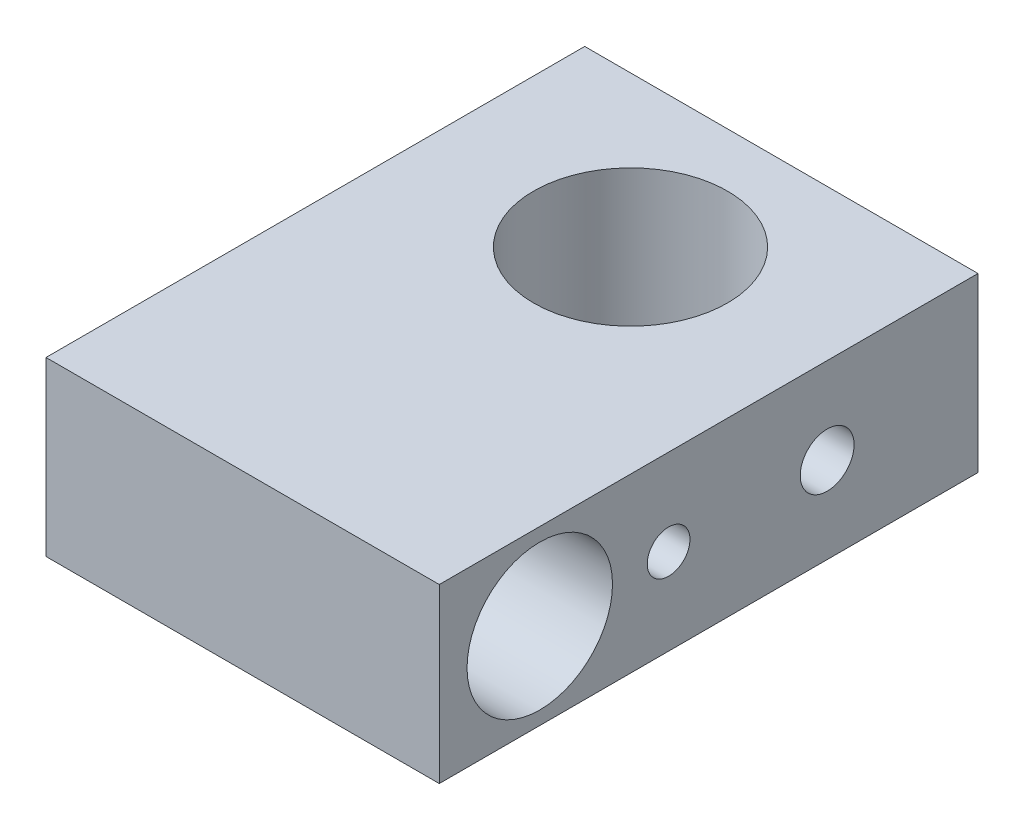
SolidWorks part; units mm, degrees
material "6061-T6 (SS)"
ref_plane "Front Plane" through (0, 0, 0) normal (0, 0, 1) x (1, 0, 0)
ref_plane "Top Plane" through (0, 0, 0) normal (0, 1, 0) x (1, 0, 0)
ref_plane "Right Plane" through (0, 0, 0) normal (1, 0, 0) x (0, 0, -1)
sketch "Sketch1" plane through (0, 0, 0) normal (0, 1, 0) x (1, 0, 0)
  line L0 (9.125, 7) -> (9.125, -18)
  line L1 (9.125, -18) -> (-9.125, -18)
  line L2 (-9.125, -18) -> (-9.125, 7)
  line L4 (-9.125, 7) -> (9.125, 7)
  line L8 (0, 0) -> (0, 7) construction
  point P4 (9.125, -18)
  point P6 (-9.125, -18)
  point P11 (-9.125, 7)
  point P12 (9.125, 7)
  dimension "D1" = 7
  dimension "D2" = 25
  dimension "D3" = 18.25
extrude "Boss-Extrude1" add sketch "Sketch1" along normal blind 8
hole_wizard "M10x1.0 Tapped Hole1" positions "Sketch3" profile "Sketch2" tap size "M10x1.0" standard "Ansi Metric" end condition through all
sketch "Sketch3" plane through (0, 8, 0) normal (0, 1, 0) x (-1, 0, 0)
  point P0 (0, 0)
sketch "Sketch2" plane through (0, 8, 0) normal (1, 0, 0) x (0, 0, 1)
  line L0 (0, 0) -> (0, 8)
  line L1 (0, 8) -> (4.5, 8)
  line L2 (4.5, 8) -> (4.5, 0)
  line L5 (4.5, 0) -> (0, 0)
  line L11 (0, -6.35) -> (0, 107.95) construction
  dimension "Thru Tap Drill Dia." = 9
  dimension "Thru Tap Drill Depth" = 8
cosmetic thread "Hole Thread1"
sketch "Sketch7" plane through (9.125, 0, 0) normal (1, 0, 0) x (0, 0, -1)
  line L0 (-18, 4) -> (-13.3362, 4) construction
  line L1 (-18, 8) -> (-18, 0) construction
  circle A0 centre (-13.3362, 4) radius 3.375
  circle A1 centre (-7.3575, 4) radius 0.9906
  dimension "D1" = 6.75
  dimension "D3" = 1.9812
  dimension "D4" = 7.3575
  dimension "D5" = 13.3362
extrude "Cut-Extrude2" cut sketch "Sketch7" against normal through all
hole_wizard "M3x0.5 Tapped Hole1" positions "Sketch9" profile "Sketch8" tap size "M3x0.5" standard "Ansi Metric"
sketch "Sketch9" plane through (9.125, 0, 0) normal (1, 0, 0) x (0, 0, -1)
  line L0 (0, 0) -> (0, 8) construction
  point P0 (0, 4)
sketch "Sketch8" plane through (9.125, 4, 0) normal (0, 1, 0) x (0, 0, -1)
  line L0 (0, 0) -> (0, 7.1011)
  line L1 (0, 7.1011) -> (1.25, 6.35)
  line L2 (1.25, 6.35) -> (1.25, 0)
  line L5 (1.25, 0) -> (0, 0)
  line L10 (0, 7.1011) -> (-1.25, 6.35) construction
  line L11 (0, -6.35) -> (0, 107.95) construction
  dimension "Tap Drill Dia." = 2.5
  dimension "Tap Drill Depth" = 6.35
  dimension "Drill Angle" = 118
cosmetic thread "Hole Thread2"
